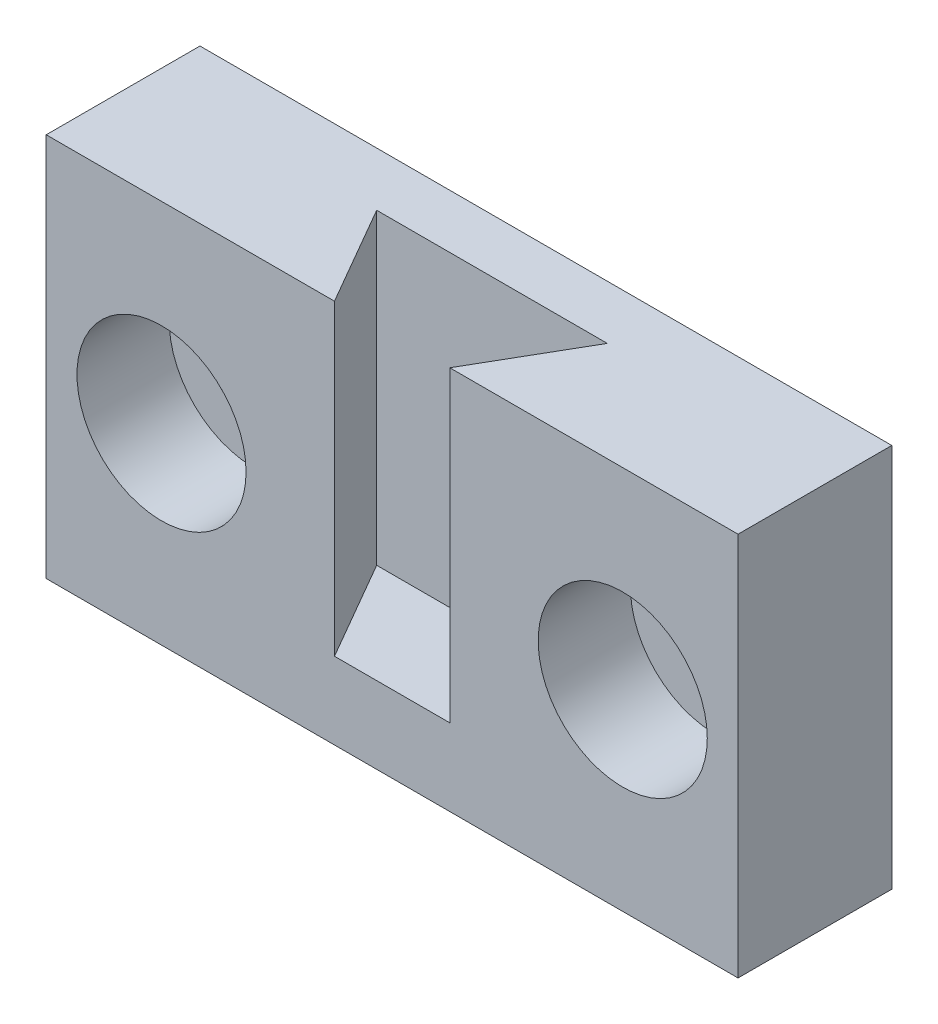
SolidWorks part; units mm, degrees
ref_plane "Front Plane" through (0, 0, 0) normal (0, 0, 1) x (1, 0, 0)
ref_plane "Top Plane" through (0, 0, 0) normal (0, 1, 0) x (1, 0, 0)
ref_plane "Right Plane" through (0, 0, 0) normal (1, 0, 0) x (0, 0, -1)
sketch "Sketch1" plane through (0, 0, 0) normal (0, 1, 0) x (1, 0, 0)
  line L0 (-9, 0) -> (9, 0)
  line L1 (9, 0) -> (9, -4)
  line L2 (9, -4) -> (1.5, -4)
  line L3 (1.5, -4) -> (3, -1.4019)
  line L4 (3, -1.4019) -> (-3, -1.4019)
  line L5 (-3, -1.4019) -> (-1.5, -4)
  line L6 (-1.5, -4) -> (-9, -4)
  line L7 (-9, -4) -> (-9, 0)
  line L8 (0, 0) -> (0, -1.4019) construction
  point P11 (6, -4)
  point P12 (-6, -4)
  point P13 (0, 0)
  point P14 (-4.079, -1.9767)
  point P15 (-2.006, -4)
  point P16 (0, -2.5475)
  dimension "D1" = 4
  dimension "D2" = 12
  dimension "D3" = 18
  dimension "D4" = 6
  dimension "D5" = 3
  dimension "D6" = 60
extrude "Boss-Extrude1" add sketch "Sketch1" along normal blind 10
sketch "Sketch2" plane through (0, 0, 0) normal (0, -1, 0) x (1, 0, 0)
  line L0 (-1.5, 4) -> (1.5, 4)
  line L1 (1.5, 4) -> (3, 1.4019)
  line L2 (3, 1.4019) -> (0.5654, 1.0718)
  line L3 (0.5654, 1.0718) -> (-3, 1.4019)
  line L4 (-3, 1.4019) -> (-1.5, 4)
  point P7 (3, 1.4019)
  point P9 (-3, 1.4019)
  point P11 (0, 0)
extrude "Boss-Extrude2" add sketch "Sketch2" against normal blind 2
hole_wizard "CBORE for M2 Hex Socket Head Cap Screw1" positions "Sketch3" profile "Sketch4" counterbore size "M2" standard "ISO" end condition through all
sketch "Sketch3" plane through (0, 0, 4) normal (0, 0, 1) x (1, 0, 0)
  line L0 (-6, 5) -> (6, 5) construction
  line L2 (0, 5) -> (0, 0) construction
  line L3 (-9, 0) -> (9, 0) construction
  line L5 (0, 5) -> (0, 10) construction
  line L7 (-9, 10) -> (-1.5, 10) construction
  point P0 (-6, 5)
  point P2 (6, 5)
  point P20 (0, 0)
  dimension "D1" = 12
sketch "Sketch4" plane through (-6, 5, 4) normal (1, 0, 0) x (0, -1, 0)
  line L0 (0, 0) -> (0, 4)
  line L1 (0, 4) -> (1.2, 4)
  line L3 (1.2, 4) -> (1.2, 2.4)
  line L4 (1.2, 2.4) -> (2.2, 2.4)
  line L5 (2.2, 2.4) -> (2.2, 0)
  line L7 (2.2, 0) -> (0, 0)
  line L11 (0, -6.35) -> (0, 107.95) construction
  dimension "Thru Hole Dia." = 2.4
  dimension "Thru Hole Depth" = 4
  dimension "C'Bore Dia." = 4.4
  dimension "C'Bore Depth" = 2.4
